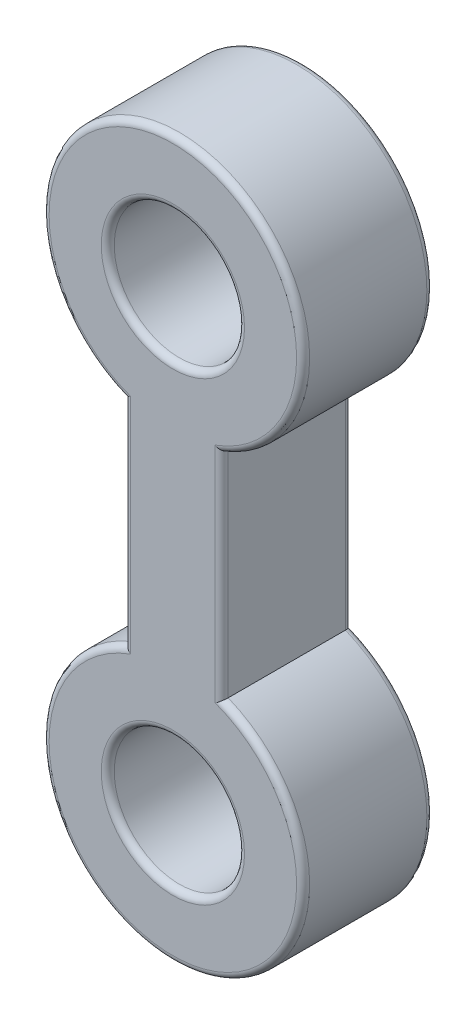
SolidWorks part; units mm, degrees
ref_plane "Front Plane" through (0, 0, 0) normal (0, 0, 1) x (1, 0, 0)
ref_plane "Top Plane" through (0, 0, 0) normal (0, 1, 0) x (1, 0, 0)
ref_plane "Right Plane" through (0, 0, 0) normal (1, 0, 0) x (0, 0, -1)
sketch "Sketch1" plane through (0, 0, 0) normal (0, 0, 1) x (1, 0, 0)
  line L0 (0, 0) -> (0, -70) construction
  line L1 (7.5, -18.5405) -> (7.5, -51.4595)
  line L2 (-7.5, -18.5405) -> (-7.5, -51.4595)
  line L3 (7.5, 0) -> (7.5, -70) construction
  circle A0 centre (0, 0) radius 10
  arc A1 (7.5, -18.5405) -> (-7.5, -18.5405) centre (0, 0) ccw
  arc A2 (-7.5, -51.4595) -> (7.5, -51.4595) centre (0, -70) ccw
  circle A3 centre (0, -70) radius 10
  dimension "D2" = 20
  dimension "D3" = 40
  dimension "D4" = 7.5
  dimension "D1" = 70
  dimension "D5" = 7.5
extrude "Boss-Extrude1" add sketch "Sketch1" along normal mid plane 20
fillet "Fillet1" radius 1 12 edges at (10, -70, -10) (10, 0, -10) (-7.5, -35, -10) (0, -90, -10) (7.5, -35, -10) (0, 20, -10) (10, -70, 10) (7.5, -35, 10) (0, -90, 10) (-7.5, -35, 10) (0, 20, 10) (10, 0, 10)
